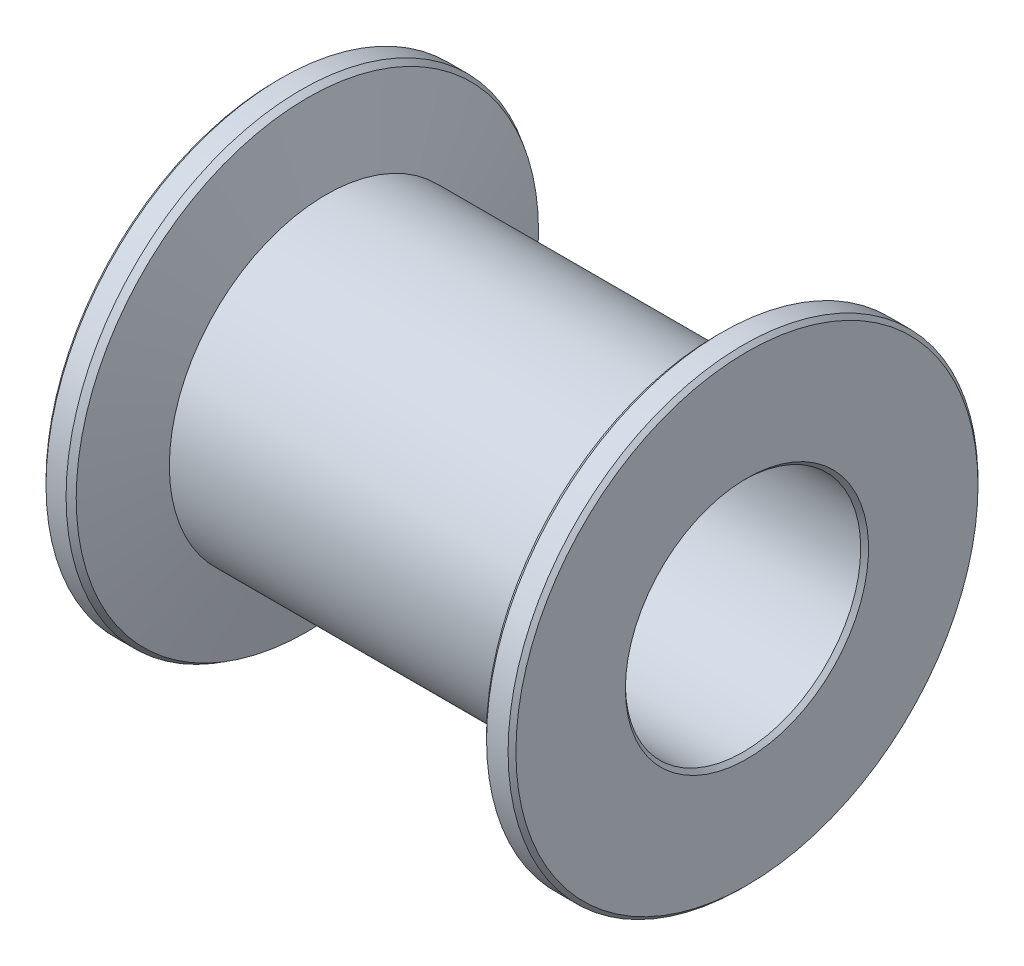
SolidWorks part; units mm, degrees
material "POM Acetal Copolymer"
ref_plane "Front Plane" through (0, 0, 0) normal (0, 0, 1) x (1, 0, 0)
ref_plane "Top Plane" through (0, 0, 0) normal (0, 1, 0) x (1, 0, 0)
ref_plane "Right Plane" through (0, 0, 0) normal (1, 0, 0) x (0, 0, -1)
ref_plane "Plane1" through (0, 0, 0) normal (0, 0, -1) x (-1, 0, 0)
sketch "Sketch1" plane through (0, 0, 0) normal (0, 0, -1) x (-1, 0, 0)
  line L0 (5.3874, 6) -> (5.2257, 5.903)
  line L1 (5.2257, 5.903) -> (4.75, 4)
  line L2 (4.75, 4) -> (-4.75, 4)
  line L3 (-4.75, 4) -> (-5.2167, 5.8667)
  line L4 (-5.2167, 5.8667) -> (-5.35, 6)
  line L5 (-5.35, 6) -> (-5.9, 6)
  line L6 (-5.9, 6) -> (-6, 5.9)
  line L7 (-6, 5.9) -> (-6, 3.105)
  line L8 (-6, 3.105) -> (-5.9, 3.005)
  line L9 (-5.9, 3.005) -> (5.9, 3.005)
  line L10 (5.9, 3.005) -> (6, 3.105)
  line L11 (6, 3.105) -> (6, 5.9)
  line L12 (6, 5.9) -> (5.9, 6)
  line L13 (5.9, 6) -> (5.3874, 6)
  line L14 (-6, 0) -> (6, 0) construction
revolve "Revolve1" add sketch "Sketch1" angle 360 about L14
